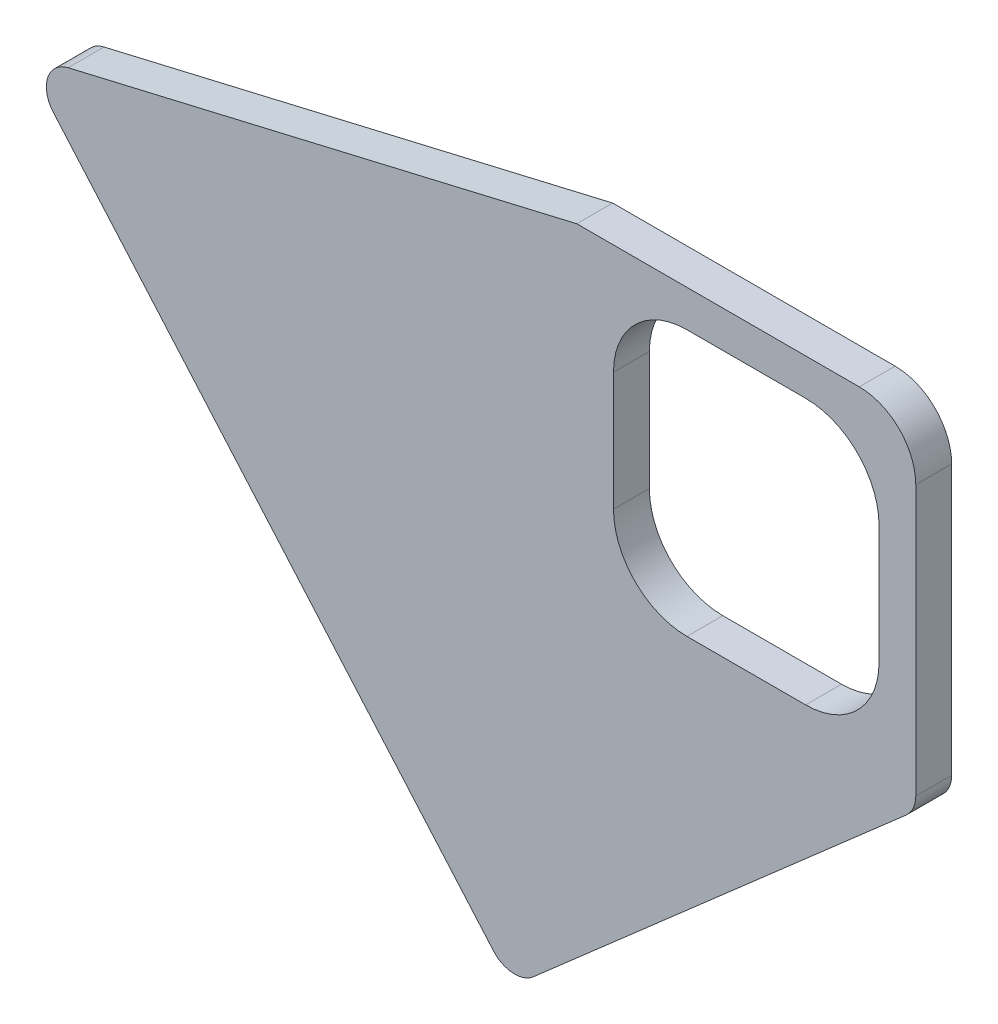
SolidWorks part; units mm, degrees
ref_plane "Front Plane" through (0, 0, 0) normal (0, 0, 1) x (1, 0, 0)
ref_plane "Top Plane" through (0, 0, 0) normal (0, 1, 0) x (1, 0, 0)
ref_plane "Right Plane" through (0, 0, 0) normal (1, 0, 0) x (0, 0, -1)
sketch "Sketch2" plane through (0, 0, 0) normal (0, 0, 1) x (1, 0, 0)
  line L0 (-30, 30) -> (30, -30) construction
  line L1 (-30, 30) -> (30, 30)
  line L4 (30, 30) -> (30, -30)
  line L5 (30, 30) -> (-41.4714, -92.5846) construction
  line L7 (-128.0968, 7.0149) -> (-30, 30)
  line L9 (-128.0968, 7.0149) -> (-41.4714, -92.5846)
  line L10 (-41.4714, -92.5846) -> (30, -30)
  point P0 (0, 0)
  dimension "D1" = 60
  dimension "D2" = 60
  dimension "D3" = 100.7536
  dimension "D4" = 132
  dimension "D5" = 95
  dimension "D6" = 141.8984
extrude "Boss-Extrude1" add sketch "Sketch2" along normal blind 6.35
fillet "Fillet1" radius 10 1 edges at (30, 30, 3.175)
fillet "Fillet2" radius 5 3 edges at (-128.0968, 7.0149, 3.175) (-41.4714, -92.5846, 3.175) (30, -30, 3.175)
sketch "Sketch3" plane through (0, 0, 6.35) normal (0, 0, 1) x (1, 0, 0)
  line L1 (-10.5, 23.5) -> (10.5, 23.5)
  line L2 (-23.5, 10.5) -> (-23.5, -10.5)
  line L3 (-10.5, -23.5) -> (10.5, -23.5)
  line L4 (23.5, 10.5) -> (23.5, -10.5)
  line L5 (-23.5, 23.5) -> (23.5, -23.5) construction
  line L6 (-23.5, -23.5) -> (23.5, 23.5) construction
  arc A0 (10.5, -23.5) -> (23.5, -10.5) centre (10.5, -10.5) ccw
  arc A1 (-23.5, -10.5) -> (-10.5, -23.5) centre (-10.5, -10.5) ccw
  arc A2 (-10.5, 23.5) -> (-23.5, 10.5) centre (-10.5, 10.5) ccw
  arc A3 (10.5, 23.5) -> (23.5, 10.5) centre (10.5, 10.5) cw
  point P0 (0, 0)
  dimension "D3" = 13
  dimension "D1" = 47
  dimension "D2" = 47
extrude "Cut-Extrude1" cut sketch "Sketch3" against normal through all
